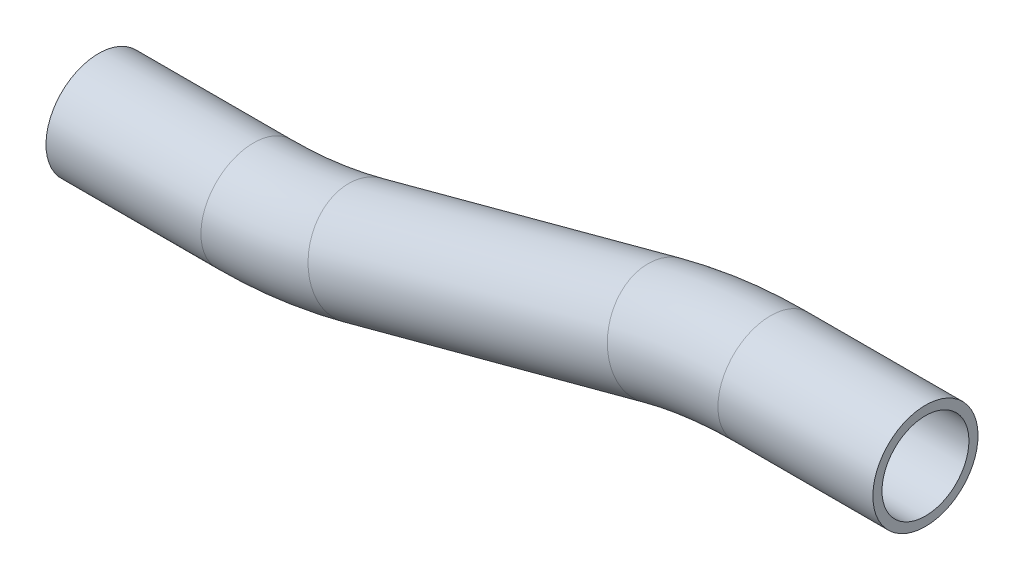
SolidWorks part; units mm, degrees
material "6061 Alloy"
ref_plane "Front Plane" through (0, 0, 0) normal (0, 0, 1) x (1, 0, 0)
ref_plane "Top Plane" through (0, 0, 0) normal (0, 1, 0) x (1, 0, 0)
ref_plane "Right Plane" through (0, 0, 0) normal (1, 0, 0) x (0, 0, -1)
sketch "Sketch1" plane through (0, 0, 0) normal (0, 0, 1) x (1, 0, 0)
  line L0 (0, 0) -> (28.0681, 0)
  line L2 (-19.722, -2.5965) -> (-73.9454, -17.1256)
  line L3 (-73.9454, -17.1256) -> (-10.0319, 0)
  line L4 (28.0681, 0) -> (-10.0319, 0)
  line L5 (-93.6674, -19.722) -> (-121.7355, -19.722)
  line L6 (-121.7355, -19.722) -> (-83.6355, -19.722)
  line L7 (-19.722, -2.5965) -> (-83.6355, -19.722)
  arc A0 (0, 0) -> (-19.722, -2.5965) centre (0, -76.2) ccw
  arc A1 (-73.9454, -17.1256) -> (-93.6674, -19.722) centre (-93.6674, 56.478) cw
  point P9 (-10.0319, 0)
  point P14 (-83.6355, -19.722)
  dimension "D3" = 15
  dimension "D4" = 15
  dimension "D1" = 76.2
  dimension "D2" = 76.2
  dimension "D5" = 76.2
  dimension "D6" = 38.1
  dimension "D7" = 38.1
ref_plane "Plane1" through (28.0681, 0, 0) normal (-1, 0, 0) x (0, 0, 1)
sketch "Sketch2" plane through (28.0681, 0, 0) normal (-1, 0, 0) x (0, 0, 1)
  circle A0 centre (0, 0) radius 9.525
  circle A1 centre (0, 0) radius 7.874
  dimension "D1" = 19.05
  dimension "D2" = 15.748
sweep "Sweep1" add profiles "Sketch2" path "Sketch1"
sketch "Sketch3" plane through (-121.7355, 0, 0) normal (-1, 0, 0) x (0, 0, 1)
  line L0 (7.874, -19.722) -> (-7.874, -19.722) construction
  circle A0 centre (0, -19.722) radius 7.874 construction
  circle A1 centre (0, -19.722) radius 7.874 construction
